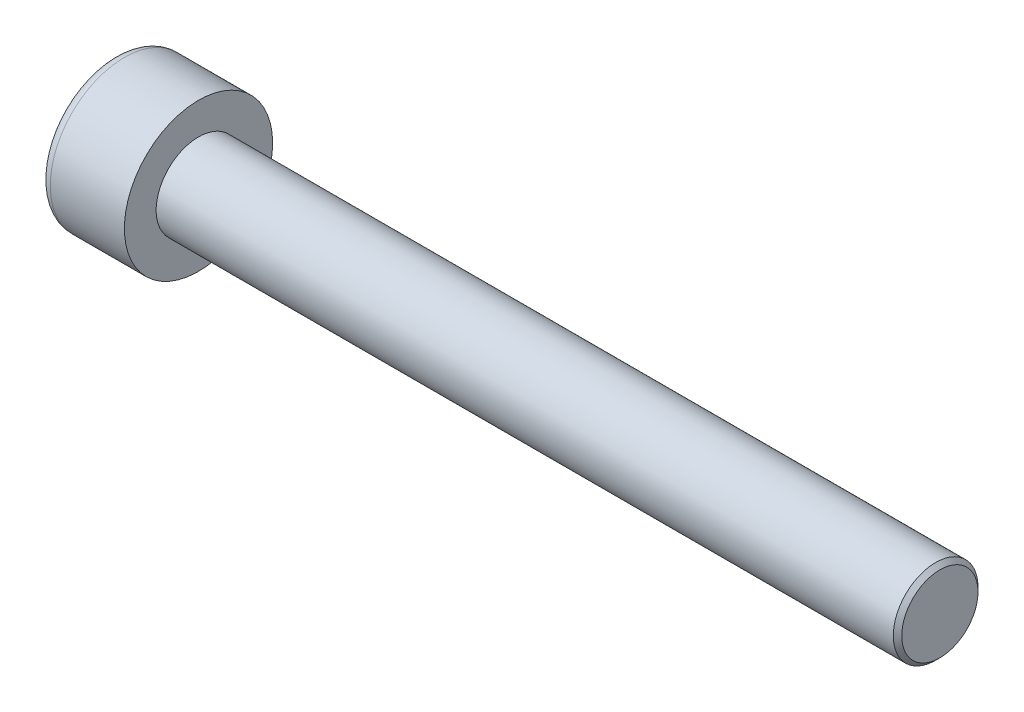
SolidWorks part; units mm, degrees
ref_plane "Front" through (0, 0, 0) normal (0, 0, 1) x (1, 0, 0)
ref_plane "Top" through (0, 0, 0) normal (0, 1, 0) x (1, 0, 0)
ref_plane "Right" through (0, 0, 0) normal (1, 0, 0) x (0, 0, -1)
sketch "Sketch1" plane through (0, 0, 0) normal (1, 0, 0) x (0, 0, -1)
  circle A0 centre (0, 0) radius 3.5
  dimension "dk" = 7
extrude "BaseHead" add sketch "Sketch1" along normal blind 4
sketch "Sketch2" plane through (4, 0, 0) normal (1, 0, 0) x (0, 0, -1)
  circle A0 centre (0, 0) radius 2
  dimension "d" = 4
extrude "BaseBody" add sketch "Sketch2" along normal blind 35
cosmetic thread "ThreadCosmetic1" parameters "b"=20, "D2"=3.242
sketch "Sketch3" plane through (0, 0, 0) normal (1, 0, 0) x (0, 0, -1)
  line L1 (1.7321, 0) -> (0.866, 1.5)
  line L2 (0.866, 1.5) -> (-0.866, 1.5)
  line L3 (-0.866, 1.5) -> (-1.7321, 0)
  line L4 (-1.7321, 0) -> (-0.866, -1.5)
  line L5 (-0.866, -1.5) -> (0.866, -1.5)
  line L6 (0.866, -1.5) -> (1.7321, 0)
  circle A0 centre (0, 0) radius 1.5 construction
  dimension "s" = 3
  dimension "e" = 3.4641
extrude "HexagonSocket" cut sketch "Sketch3" along normal blind 2
sketch "Sketch4" plane through (-4.1961, 0.75, 0) normal (0, 0, 1) x (-1, 0, 0)
  line L0 (-6.1961, 2.25) -> (-7.0622, 0.75)
  line L2 (-7.0622, 0.75) -> (-6.1961, 0.75)
  line L3 (-6.1961, 0.75) -> (-6.1961, 2.25)
  line L4 (-5.0351, 0.75) -> (0.839, 0.75) construction
  line L5 (-43.1961, 0.75) -> (-8.1961, 0.75) construction
  line L6 (-8.1961, 0.75) -> (-4.1961, 0.75) construction
  dimension "m" = 60
revolve "Cut-Revolve1" cut sketch "Sketch4" angle 360 about L4
fillet "HeadFillet" [suppressed] radius 0.2
fillet "TopFillet" radius 0.5 1 edges at (0, 0, -3.5)
chamfer "Chamfer1" distance 0.2 angle 45 1 edges at (39, 0, -2)
sketch "Sketch5" plane through (0, 0, 0) normal (0, 0, 1) x (1, 0, 0)
  line L0 (38.8, 1.6718) -> (38.9895, 2)
  line L1 (38.9895, 2) -> (38.9895, 2.379)
  line L2 (38.9895, 2.379) -> (38.6105, 2.379)
  line L3 (38.6105, 2.379) -> (38.6105, 2)
  line L4 (38.6105, 2) -> (38.8, 1.6718)
  line L5 (0, 0) -> (7.8886, 0) construction
  line L6 (38.8, -2) -> (38.8, 2) construction
  dimension "D1" = 4
  dimension "D2" = 0.379
revolve "Cut-Revolve10" [suppressed] cut sketch "Sketch5" angle 360 about L5
pattern_linear "LPattern10" [suppressed] count 44 spacing 0.4548 along (1, 0, 0)
equation "\"r1@TopFillet\" = \"d@Sketch2\" / 8"
equation "\"D1@Chamfer1\" = \"r@HeadFillet\""
equation "\"D1@Sketch5\" = \"d@Sketch2\""
equation "\"D2@Sketch5\" =  ( \"d@Sketch2\" - \"D2@ThreadCosmetic1\" )  / 2"
equation "\"D3@LPattern10\" = \"D2@Sketch5\" * 1.2"
equation "\"D1@LPattern10\" = \"b@ThreadCosmetic1\" / \"D3@LPattern10\""
